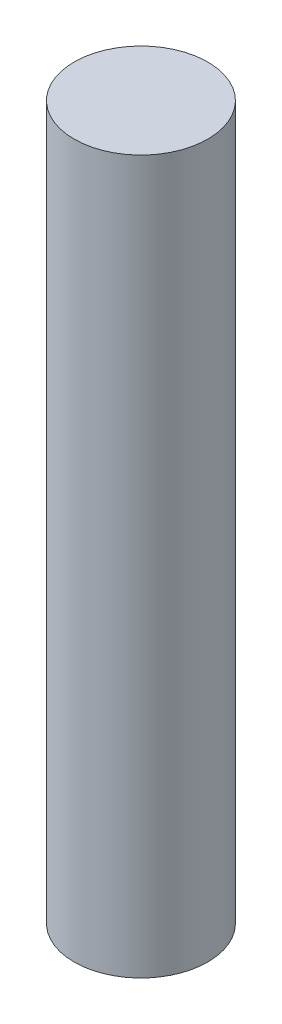
SolidWorks part; units mm, degrees
ref_plane "Front" through (0, 0, 0) normal (0, 0, 1) x (1, 0, 0)
ref_plane "Top" through (0, 0, 0) normal (0, 1, 0) x (1, 0, 0)
ref_plane "Right" through (0, 0, 0) normal (1, 0, 0) x (0, 0, -1)
sketch "Sketch1" plane through (0, 0, 0) normal (0, 1, 0) x (1, 0, 0)
  circle A0 centre (0, 0) radius 1.5
  dimension "D1" = 3
extrude "Boss-Extrude1" add sketch "Sketch1" along normal mid plane 16
